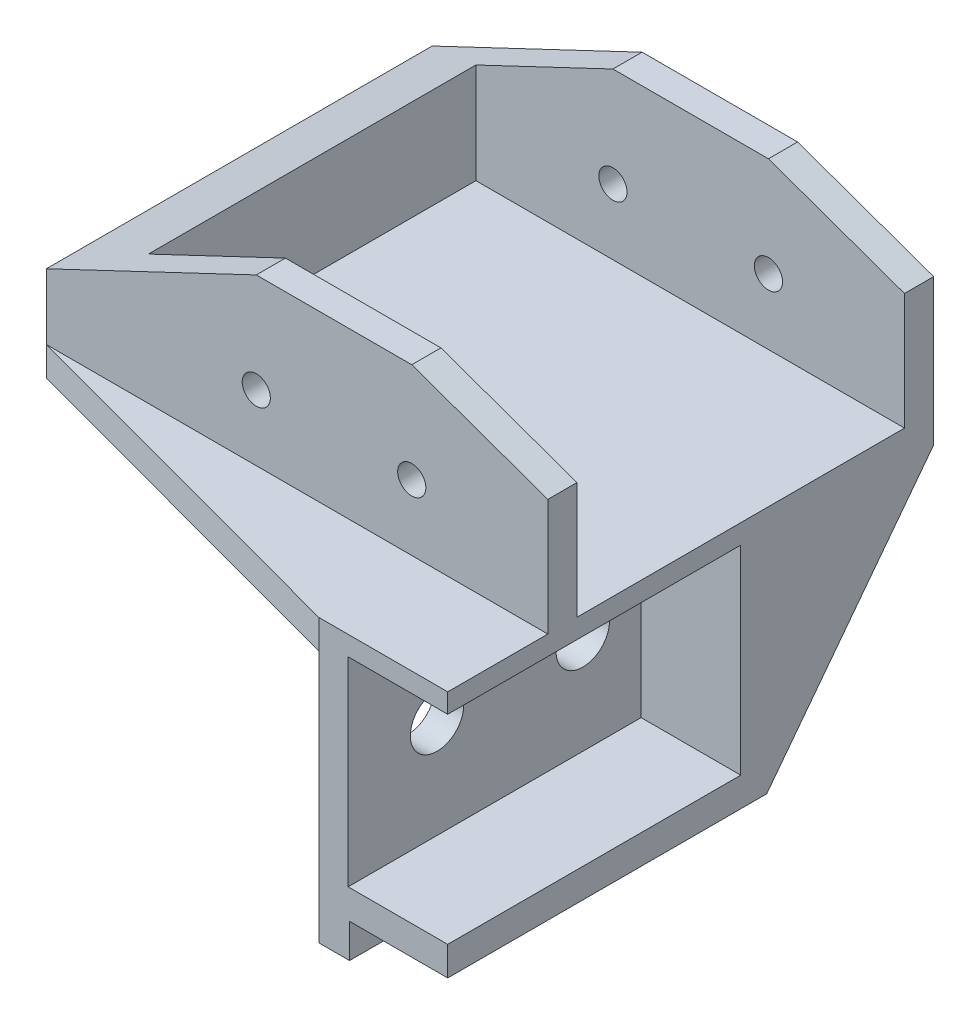
SolidWorks part; units mm, degrees
ref_plane "前视基准面" through (0, 0, 0) normal (0, 0, 1) x (1, 0, 0)
ref_plane "上视基准面" through (0, 0, 0) normal (0, 1, 0) x (1, 0, 0)
ref_plane "右视基准面" through (0, 0, 0) normal (1, 0, 0) x (0, 0, -1)
sketch "草图1" plane through (0, 0, 0) normal (0, 0, 1) x (1, 0, 0)
  line L0 (0, 0) -> (-103.2, 0)
  line L1 (-103.2, 0) -> (-103.2, 20)
  line L2 (-103.2, 20) -> (0, 20)
  line L3 (0, 20) -> (0, 0)
  dimension "D1" = 103.2
  dimension "D2" = 20
extrude "凸台-拉伸1" add sketch "草图1" along normal blind 39.7
sketch "草图2" plane through (0, 20, 0) normal (0, 1, 0) x (1, 0, 0)
  line L0 (-51.6, 0) -> (-51.6, -39.7) construction
  line L2 (-99.2, -19.85) -> (-72.6862, -19.85) construction
  line L5 (-95.7, -3) -> (-7.5, -3)
  line L6 (-95.7, -3) -> (-95.7, -36.7)
  line L7 (-95.7, -36.7) -> (-7.5, -36.7)
  line L8 (-7.5, -3) -> (-7.5, -36.7)
  dimension "D1" = 88.2
  dimension "D2" = 33.7
extrude "切除-拉伸1" cut sketch "草图2" against normal offset from surface (17 mm away) 3 up to face at (-51.6, 0, 19.85)
sketch "草图3" plane through (0, 0, 0) normal (0, -1, 0) x (1, 0, 0)
  line L6 (-51.6, 39.7) -> (-51.6, -13.7739) construction
  line L11 (-103.2, 0) -> (0, 0) construction
  line L12 (-64.85, 0) -> (-38.35, 0)
  line L15 (-64.85, 0) -> (-64.85, 50)
  line L16 (-64.85, 50) -> (-38.35, 50)
  line L17 (-38.35, 50) -> (-38.35, 0)
  point P11 (-51.6, 0)
  dimension "D1" = 50
  dimension "D2" = 13.25
extrude "凸台-拉伸2" add sketch "草图3" along normal blind 29 from offset 3 offset against normal yes
sketch "草图21" plane through (0, 0, 50) normal (0, 0, 1) x (1, 0, 0)
  line L0 (-7.5, 3) -> (-95.7, 3) construction
  line L1 (-7.5, 3) -> (-95.7, 3) construction
  line L2 (-98.033, -9.25) -> (-9.0097, -9.25) construction
  line L3 (-51.6, -26) -> (-51.6, 30.6239) construction
  line L4 (-61.85, 1) -> (-41.35, 1)
  line L5 (-61.85, 1) -> (-61.85, -19.5)
  line L6 (-61.85, -19.5) -> (-41.35, -19.5)
  line L7 (-41.35, 1) -> (-41.35, -19.5)
  dimension "D1" = 12.25
  dimension "D2" = 20.5
  dimension "D3" = 20.5
extrude "切除-拉伸11" cut sketch "草图21" against normal offset from surface (30.15 mm away) 19.85 up to face at (-51.6, -1.5, 0)
sketch "草图22" plane through (0, -26, 0) normal (0, -1, 0) x (1, 0, 0)
  line L1 (-61.7, 50) -> (-41.5, 50)
  line L2 (-41.5, 50) -> (-41.5, 0)
  line L3 (-64.85, 0) -> (-38.35, 0) construction
  line L4 (-41.5, 0) -> (-61.7, 0)
  line L5 (-61.7, 0) -> (-61.7, 50)
  line L6 (-38.35, 50) -> (-64.85, 50) construction
  dimension "D1" = 0
extrude "切除-拉伸12" cut sketch "草图22" against normal offset from surface (3.5 mm away) 3 up to face at (-51.6, -19.5, 34.925)
sketch "草图24" plane through (-38.35, 0, 0) normal (1, 0, 0) x (0, 0, -1)
  line L0 (0, 0) -> (0, -26)
  line L1 (0, -26) -> (-19.85, -26)
  line L2 (0, -26) -> (-50, -26) construction
  line L3 (-19.85, -26) -> (0, 0)
  line L4 (-19.85, -19.5) -> (-19.85, 1) construction
  line L5 (-19.85, -19.5) -> (-19.85, 1) construction
extrude "切除-拉伸14" cut sketch "草图24" against normal through all
sketch "草图25" plane through (0, 0, 0) normal (0, -1, 0) x (1, 0, 0)
  line L0 (-38.35, 39.7) -> (-38.35, 50)
  line L1 (-38.35, 50) -> (0, 39.7)
  line L2 (-51.6, 50) -> (-51.6, 41.294) construction
  line L4 (-38.35, 39.7) -> (0, 39.7)
  line L5 (-64.85, 39.7) -> (-103.2, 39.7)
  line L6 (-64.85, 50) -> (-103.2, 39.7)
  line L7 (-64.85, 39.7) -> (-64.85, 50)
extrude "凸台-拉伸4" add sketch "草图25" against normal up to surface (3 mm away) up to face at (-51.6, 3, 44.85)
hole_wizard "M2.5 间隙孔1" positions "草图26" profile "草图27" hole size "M2.5" standard "ISO" end condition through all
sketch "草图26" plane through (0, 0, 0) normal (0, 0, -1) x (-1, 0, 0)
  line L0 (-2.4764, 3) -> (110.5641, 3) construction
  line L2 (38.35, 0) -> (0, 0) construction
  line L3 (51.6, 0) -> (51.6, 22.298) construction
  point P8 (37.6, 9.75)
  point P10 (21.6, 9.75)
  point P23 (65.6, 9.75)
  point P24 (81.6, 9.75)
  dimension "D1" = 3
  dimension "D2" = 14
  dimension "D3" = 16
  dimension "D4" = 6.75
  dimension "D5" = 6.75
sketch "草图27" plane through (-81.6, 9.75, 0) normal (1, 0, 0) x (0, 1, 0)
  line L0 (0, 0) -> (0, 50)
  line L1 (0, 50) -> (1.45, 50)
  line L2 (1.45, 50) -> (1.45, 0.025)
  line L3 (1.45, 0.025) -> (1.475, 0)
  line L5 (1.475, 0) -> (0, 0)
  line L6 (-1.45, 0.025) -> (-1.475, 0) construction
  line L11 (0, -6.35) -> (0, 107.95) construction
  dimension "通孔孔直径" = 2.9
  dimension "通孔孔深度" = 50
  dimension "近端锥形沉头孔直径" = 2.95
  dimension "近端锥形沉头孔角度" = 90
hole_wizard "M5 间隙孔2" positions "草图34" profile "草图33" hole size "M5" standard "ISO" end condition through all
sketch "草图34" plane through (-38.35, 0, 0) normal (1, 0, 0) x (0, 0, -1)
  line L2 (-43.9538, -9.25) -> (-19.6706, -9.25) construction
  line L5 (-19.85, 0.85) -> (-19.85, -19.35) construction
  line L7 (-19.85, 1) -> (-50, 1) construction
  point P10 (-25.85, -9.25)
  point P21 (-40.85, -9.25)
  dimension "D1" = 6
  dimension "D2" = 15
sketch "草图33" plane through (-38.35, -9.25, 40.85) normal (0, 1, 0) x (0, 0, -1)
  line L0 (0, 0) -> (0, 64.85)
  line L1 (0, 64.85) -> (2.75, 64.85)
  line L2 (2.75, 64.85) -> (2.75, 0.025)
  line L3 (2.75, 0.025) -> (2.775, 0)
  line L5 (2.775, 0) -> (0, 0)
  line L6 (-2.75, 0.025) -> (-2.775, 0) construction
  line L11 (0, -6.35) -> (0, 107.95) construction
  dimension "通孔孔直径" = 5.5
  dimension "通孔孔深度" = 64.85
  dimension "近端锥形沉头孔直径" = 5.55
  dimension "近端锥形沉头孔角度" = 90
sketch "草图35" plane through (0, 0, 0) normal (0, 0, -1) x (-1, 0, 0)
  line L0 (21.6, 9.75) -> (37.6, 9.75) construction
  line L1 (21.6, 9.75) -> (21.6, 21.6918) construction
  line L2 (37.6, 9.75) -> (37.6, 21.6918) construction
  line L3 (0, 9.75) -> (21.6, 20)
  line L4 (0, 0) -> (0, 20) construction
  line L5 (21.6, 20) -> (0, 20)
  line L6 (0, 20) -> (0, 9.75)
  line L7 (0, 20) -> (103.2, 20) construction
  line L8 (51.6, 0) -> (51.6, 24.4852) construction
  line L10 (37.6, 20) -> (51.6, 15)
  line L11 (51.6, 15) -> (51.6, 20)
  line L12 (65.6, 20) -> (37.6, 20)
  line L13 (81.6, 20) -> (103.2, 20)
  line L14 (103.2, 9.75) -> (81.6, 20)
  line L15 (103.2, 20) -> (103.2, 9.75)
  line L16 (65.6, 20) -> (51.6, 15)
  line M17 (103.2, 0) -> (103.2, 20)
  line M18 (103.2, 20) -> (0, 20)
  dimension "D1" = 5
extrude "切除-拉伸19" cut sketch "草图35" against normal through all contours L14 M17 M18 | L6 L3 L5 | L16 L12 L10
ref_plane "基准面1" through (-51.6, 0, 0) normal (-1, 0, 0) x (0, 0, 1)
sketch "草图36" plane through (-51.6, 0, 0) normal (-1, 0, 0) x (0, 0, 1)
  line L1 (0, 20) -> (50, 20)
  line L2 (0, 20) -> (0, -26)
  line L3 (0, -26) -> (50, -26)
  line L4 (50, 20) -> (50, -26)
extrude "切除-拉伸20" cut sketch "草图36" against normal up to surface (51.6 mm away) up to face at (0, 4.5, 23.82)
ref_plane "Plane1" through (0, -9.25, 0) normal (0, 1, 0) x (1, 0, 0)
